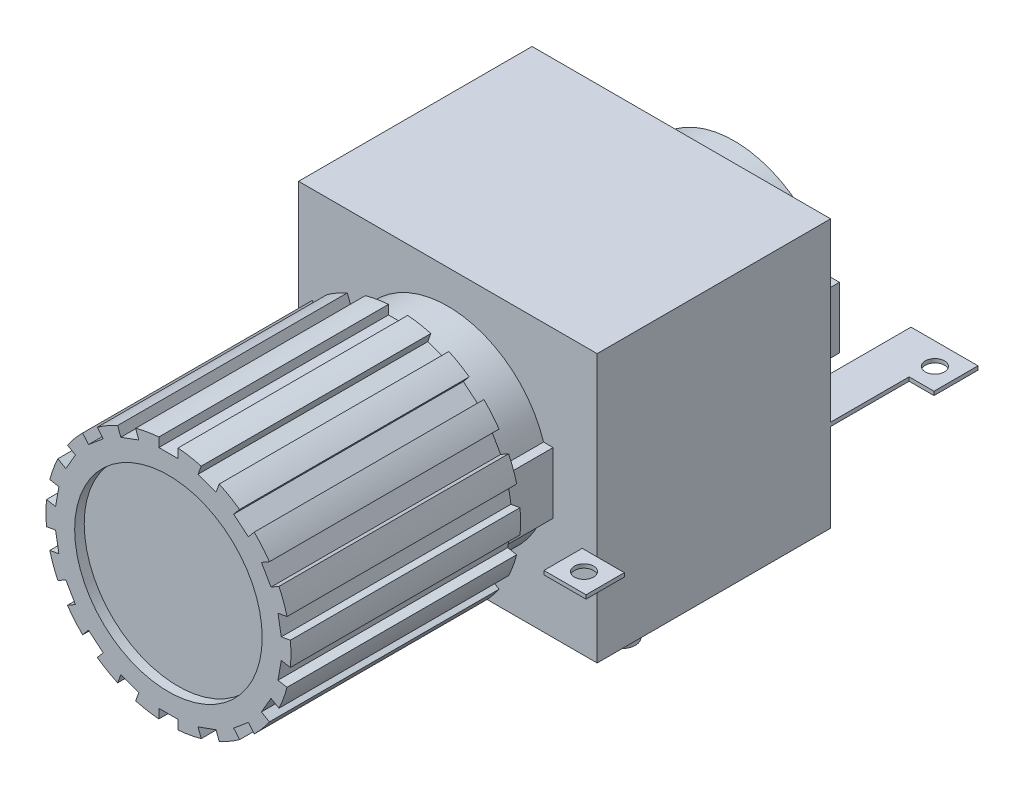
SolidWorks part; units mm, degrees
ref_plane "Alzado" through (0, 0, 0) normal (0, 0, 1) x (1, 0, 0)
ref_plane "Planta" through (0, 0, 0) normal (0, 1, 0) x (1, 0, 0)
ref_plane "Vista lateral" through (0, 0, 0) normal (1, 0, 0) x (0, 0, -1)
sketch "Croquis1" plane through (0, 0, 0) normal (0, 0, 1) x (1, 0, 0)
  circle A0 centre (0, 0) radius 32
  dimension "D1" = 64
extrude "Saliente-Extruir1" add sketch "Croquis1" along normal blind 60
sketch "Croquis2" plane through (0, 0, 60) normal (0, 0, 1) x (1, 0, 0)
  circle A0 centre (0, 0) radius 24.5
  dimension "D1" = 49
extrude "Cortar-Extruir1" cut sketch "Croquis2" against normal blind 2.5
sketch "Croquis3" plane through (0, 0, 60) normal (0, 0, 1) x (1, 0, 0)
  line L1 (-2.5, 34.5) -> (2.5, 34.5)
  line L2 (-2.5, 34.5) -> (-2.5, 29.5)
  line L3 (-2.5, 29.5) -> (2.5, 29.5)
  line L4 (2.5, 34.5) -> (2.5, 29.5)
  line L5 (-2.5, 34.5) -> (2.5, 29.5) construction
  line L6 (-2.5, 29.5) -> (2.5, 34.5) construction
  circle A0 centre (0, 0) radius 32 construction
  point P0 (0, 32)
  dimension "D1" = 5
  dimension "D2" = 5
extrude "Cortar-Extruir2" cut sketch "Croquis3" against normal through all
pattern_circular "MatrizC1" count 18 over 360 about axis through (0, 0, 0) along (0, 0, 1) of "Cortar-Extruir2"
sketch "Croquis4" plane through (0, 0, 0) normal (0, 0, -1) x (-1, 0, 0)
  circle A0 centre (0, 0) radius 26.25
  dimension "D1" = 52.5
extrude "Saliente-Extruir2" add sketch "Croquis4" along normal blind 87.8
sketch "Croquis5" plane through (0, 0, -87.8) normal (0, 0, -1) x (-1, 0, 0)
  circle A0 centre (0, 0) radius 22.75
  circle A1 centre (0, 0) radius 26.25 construction
  dimension "D1" = 3.5
extrude "Cortar-Extruir3" cut sketch "Croquis5" against normal blind 37
sketch "Croquis6" plane through (0, 0, -87.8) normal (0, 0, -1) x (-1, 0, 0)
  line L0 (0, 0) -> (-26.25, 0) construction
  line L2 (-27.5, 8) -> (-25, 8)
  line L3 (-27.5, 8) -> (-27.5, -8)
  line L4 (-27.5, -8) -> (-25, -8)
  line L5 (-25, 8) -> (-25, -8)
  line L6 (-27.5, 8) -> (-25, -8) construction
  line L7 (-27.5, -8) -> (-25, 8) construction
  circle A0 centre (0, 0) radius 26.25 construction
  dimension "D1" = 2.5
  dimension "D2" = 16
extrude "Saliente-Extruir3" add sketch "Croquis6" against normal up to next
ref_plane "Plano1" through (0, 0, -13) normal (0, 0, -1) x (-1, 0, 0)
sketch "Croquis7" plane through (0, 0, -13) normal (0, 0, -1) x (-1, 0, 0)
  line L1 (-39, 35) -> (39, 35)
  line L2 (-39, 35) -> (-39, -35)
  line L3 (-39, -35) -> (39, -35)
  line L4 (39, 35) -> (39, -35)
  line L5 (-39, 35) -> (39, -35) construction
  line L6 (-39, -35) -> (39, 35) construction
  point P0 (0, 0)
  dimension "D1" = 78
  dimension "D2" = 70
extrude "Saliente-Extruir4" add sketch "Croquis7" along normal blind 61
sketch "Croquis8" plane through (-39, 0, 0) normal (-1, 0, 0) x (0, 0, 1)
  line L0 (-74, 35) -> (-13, 35) construction
  line L1 (-59.8, -11) -> (-69.8, -11)
  line L2 (-59.8, -11) -> (-59.8, -12)
  line L3 (-59.8, -12) -> (-69.8, -12)
  line L4 (-69.8, -11) -> (-69.8, -12)
  line L5 (-3, -7) -> (-13, -7)
  line L6 (-3, -7) -> (-3, -8)
  line L7 (-3, -8) -> (-13, -8)
  line L8 (-13, -7) -> (-13, -8)
  line L9 (-13, -35) -> (-13, 35) construction
  line L10 (-74, -35) -> (-74, 35) construction
  dimension "D1" = 10
  dimension "D2" = 10
  dimension "D3" = 1
  dimension "D4" = 1
  dimension "D5" = 47
  dimension "D6" = 43
  dimension "D7" = 14.2
extrude "Saliente-Extruir5" add sketch "Croquis8" along normal blind 11.5
sketch "Croquis9" plane through (-39, 0, 0) normal (-1, 0, 0) x (0, 0, 1)
  line L0 (-13, -35) -> (-13, 35) construction
  line L1 (-3, -8) -> (-13, -8)
  line L2 (-3, -8) -> (-3, 5)
  line L3 (-3, 5) -> (-13, 5)
  line L4 (-13, -8) -> (-13, 5)
  dimension "D1" = 13
extrude "Saliente-Extruir6" add sketch "Croquis9" against normal blind 1
ref_plane "Plano2" through (0, -11, 0) normal (0, -1, 0) x (-1, 0, 0)
sketch "Croquis10" plane through (0, -11, 0) normal (0, -1, 0) x (-1, 0, 0)
  line L0 (39, 13) -> (-39, 13) construction
  line L1 (-35.1, 13) -> (-46.1, 13)
  line L2 (-35.1, 13) -> (-35.1, 3)
  line L3 (-35.1, 3) -> (-46.1, 3)
  line L4 (-46.1, 13) -> (-46.1, 3)
  line L6 (-27.5, 0) -> (-27.5, 13) construction
  dimension "D1" = 11
  dimension "D2" = 10
  dimension "D3" = 7.6
extrude "Saliente-Extruir7" add sketch "Croquis10" along normal blind 1
sketch "Croquis11" plane through (0, -11, 0) normal (0, -1, 0) x (-1, 0, 0)
  line L1 (-39, 74) -> (-28, 74)
  line L2 (-39, 74) -> (-39, 94.5)
  line L3 (-45.5, 106) -> (-28, 106)
  line L4 (-28, 74) -> (-28, 106)
  line L7 (-39, 94.5) -> (-45.5, 94.5)
  line L8 (-45.5, 106) -> (-45.5, 94.5)
  dimension "D1" = 32
  dimension "D2" = 17.5
  dimension "D3" = 6.5
  dimension "D4" = 11.5
extrude "Saliente-Extruir8" add sketch "Croquis11" along normal blind 1
sketch "Croquis12" plane through (0, -7, 0) normal (0, 1, 0) x (1, 0, 0)
  circle A0 centre (-44.75, 7.9491) radius 2.5
  dimension "D1" = 5
extrude "Cortar-Extruir4" cut sketch "Croquis12" against normal through all
sketch "Croquis13" plane through (0, -11, 0) normal (0, 1, 0) x (1, 0, 0)
  circle A0 centre (40.6, 7.9786) radius 2.5
  dimension "D1" = 5
extrude "Cortar-Extruir5" cut sketch "Croquis13" against normal blind 1
sketch "Croquis14" plane through (0, -11, 0) normal (0, 1, 0) x (1, 0, 0)
  circle A0 centre (-44.75, 65.0495) radius 2.5
  dimension "D1" = 5
extrude "Cortar-Extruir6" cut sketch "Croquis14" against normal blind 1
sketch "Croquis15" plane through (0, -11, 0) normal (0, 1, 0) x (1, 0, 0)
  line L0 (45.5, 100.25) -> (40, 100.25) construction
  line L1 (45.5, 106) -> (45.5, 94.5) construction
  circle A0 centre (40, 100.25) radius 2.5
  dimension "D1" = 5
  dimension "D2" = 5.5
extrude "Cortar-Extruir7" cut sketch "Croquis15" against normal blind 1
sketch "Croquis16" plane through (0, -35, 0) normal (0, -1, 0) x (-1, 0, 0)
  line L0 (-39, 74) -> (-39, 13) construction
  line L1 (-39, 13) -> (39, 13) construction
  circle A0 centre (-26.5, 32) radius 3.5
  dimension "D1" = 7
  dimension "D2" = 12.5
  dimension "D3" = 19
extrude "Saliente-Extruir9" add sketch "Croquis16" along normal blind 10
